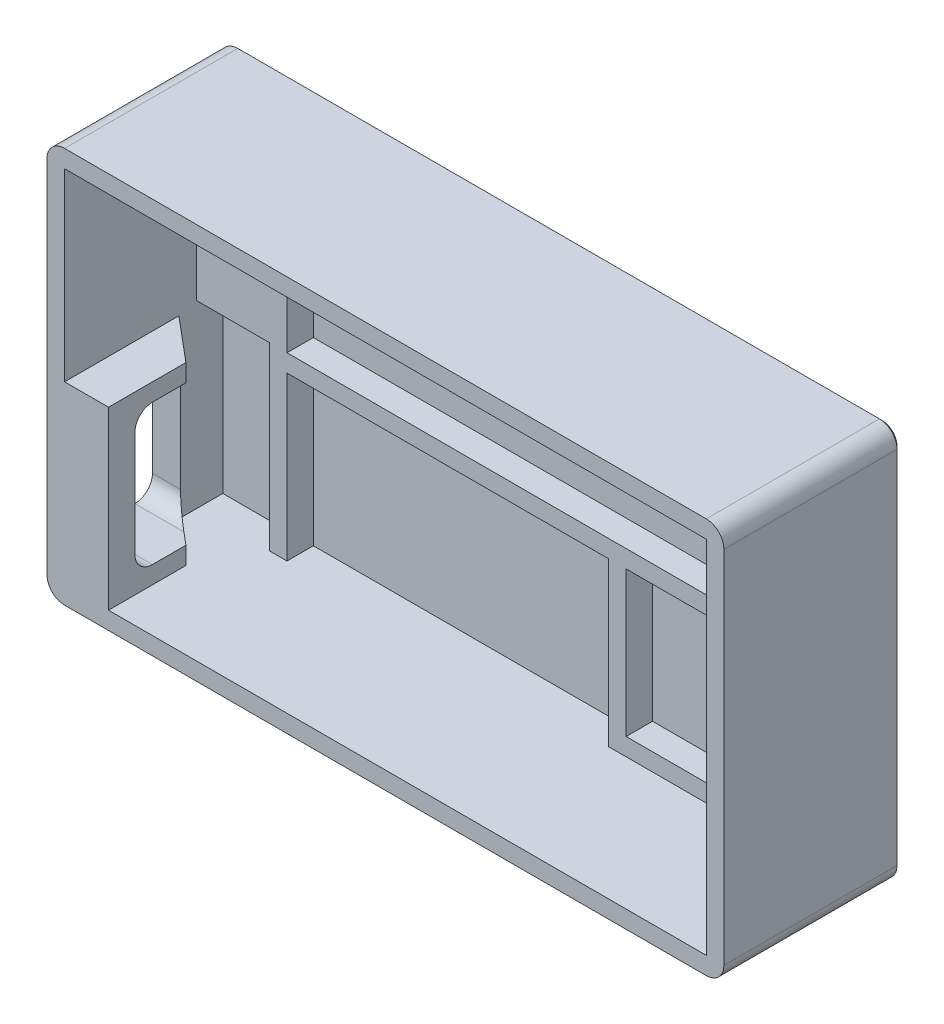
SolidWorks part; units mm, degrees
material "Custom Plastic"
ref_plane "Front Plane" through (0, 0, 0) normal (0, 0, 1) x (1, 0, 0)
ref_plane "Top Plane" through (0, 0, 0) normal (0, 1, 0) x (1, 0, 0)
ref_plane "Right Plane" through (0, 0, 0) normal (1, 0, 0) x (0, 0, -1)
sketch "Sketch1" plane through (0, 0, 0) normal (0, 0, 1) x (1, 0, 0)
  line L0 (47.9984, -22.6009) -> (51.1988, -25.8013) construction
  line L1 (51.1988, -22.6009) -> (47.9984, -25.8013) construction
  line L2 (8.5014, -16.2535) -> (10.4978, -18.2499) construction
  line L3 (10.4978, -16.2535) -> (8.5014, -18.2499) construction
  line L4 (30.1981, -17.239) -> (31.7221, -18.763) construction
  line L5 (31.7221, -17.239) -> (30.1981, -18.763) construction
  line L8 (30.1981, -17.239) -> (30.1981, -18.763)
  line L9 (30.1981, -18.763) -> (31.7221, -18.763)
  line L10 (31.7221, -18.763) -> (31.7221, -17.239)
  line L11 (31.7221, -17.239) -> (30.1981, -17.239)
  line L12 (10.4978, -16.2535) -> (8.5014, -16.2535)
  line L13 (8.5014, -16.2535) -> (8.5014, -18.2499)
  line L14 (8.5014, -18.2499) -> (10.4978, -18.2499)
  line L15 (10.4978, -18.2499) -> (10.4978, -16.2535)
  line L16 (47.9984, -22.6009) -> (47.9984, -25.8013)
  line L17 (47.9984, -25.8013) -> (51.1988, -25.8013)
  line L18 (51.1988, -25.8013) -> (51.1988, -22.6009)
  line L19 (51.1988, -22.6009) -> (47.9984, -22.6009)
  line L1295 (-5.0013, 10.0001) -> (66.9987, 10.0001)
  line L1296 (-5.0013, 10.0001) -> (-5.0013, -29.9999)
  line L1297 (-5.0013, -29.9999) -> (66.9987, -29.9999)
  line L1298 (66.9987, 10.0001) -> (66.9987, -29.9999)
  circle A0 centre (33.5001, -18.001) radius 0.762
  circle A1 centre (36.0401, -18.001) radius 0.762
  circle A2 centre (53.5203, -7.5108) radius 1.4478
  circle A3 centre (49.3217, -7.5108) radius 1.4478
  circle A4 centre (45.1206, -7.5108) radius 1.4478
  circle A5 centre (40.9219, -7.5108) radius 1.4478
  circle A6 centre (36.7208, -7.5108) radius 1.4478
  circle A7 centre (32.5222, -7.5108) radius 1.4478
  circle A8 centre (28.3235, -7.5108) radius 1.4478
  circle A9 centre (24.1249, -7.5108) radius 1.4478
  circle A10 centre (19.9238, -7.5108) radius 1.4478
  circle A11 centre (15.7251, -7.5108) radius 1.4478
  circle A12 centre (11.524, -7.5108) radius 1.4478
  circle A13 centre (7.3228, -7.5108) radius 1.4478
  circle A14 centre (53.5203, -2.0117) radius 1.4478
  circle A15 centre (49.3217, -2.0117) radius 1.4478
  circle A16 centre (45.1206, -2.0117) radius 1.4478
  circle A17 centre (40.9219, -2.0117) radius 1.4478
  circle A18 centre (36.7208, -2.0117) radius 1.4478
  circle A19 centre (32.5222, -2.0117) radius 1.4478
  circle A20 centre (28.3235, -2.0117) radius 1.4478
  circle A21 centre (24.1249, -2.0117) radius 1.4478
  circle A22 centre (19.9238, -2.0117) radius 1.4478
  circle A23 centre (15.7251, -2.0117) radius 1.4478
  circle A24 centre (11.524, -2.0117) radius 1.4478
  circle A25 centre (7.3228, -2.0117) radius 1.4478
  circle A26 centre (7.3076, 4.699) radius 0.889
  circle A27 centre (25.0876, 4.699) radius 0.889
  circle A28 centre (53.3883, 4.8997) radius 0.889
  circle A29 centre (35.6083, 4.8997) radius 0.889
  circle A30 centre (26.0985, -19.0906) radius 0.6985
  circle A31 centre (26.0985, -26.7106) radius 0.6985
  circle A32 centre (20.4978, -19.0906) radius 0.6985
  circle A33 centre (20.4978, -26.7106) radius 0.6985
  circle A34 centre (26.0985, -14.031) radius 0.8382
  circle A35 centre (26.0985, -16.571) radius 0.8382
  circle A36 centre (20.4978, -13.9319) radius 0.8382
  circle A37 centre (20.4978, -16.4719) radius 0.8382
  circle A38 centre (9.4996, -24.7498) radius 1.2497
  circle A39 centre (-0.0013, 0.0001) radius 3.0988
  circle A40 centre (61.9987, -19.9999) radius 3.0988
  circle A41 centre (53.7997, -24.2011) radius 1.6002
  circle A42 centre (49.5986, -18.702) radius 1.6002
  circle A43 centre (53.7997, -18.702) radius 1.6002
  dimension "D1" = 62
  dimension "D2" = 72
  dimension "D3" = 40
  dimension "D4" = 5
  dimension "D5" = 10
  dimension "D6" = 20
sketch "Sketch2" plane through (0, 0, 0) normal (0, 0, 1) x (1, 0, 0)
  line L0 (-5.0013, 10.0001) -> (-5.5013, 10.5001) construction
  line L1 (-5.5013, 10.5001) -> (67.4987, 10.5001) construction
  line L2 (-5.5013, 10.5001) -> (-5.5013, -30.4999) construction
  line L3 (-5.5013, -30.4999) -> (67.4987, -30.4999) construction
  line L4 (67.4987, 10.5001) -> (67.4987, -30.4999) construction
  line L5 (-7.5013, 12.5001) -> (69.4987, 12.5001)
  line L6 (-7.5013, 12.5001) -> (-7.5013, -32.4999)
  line L7 (-7.5013, -32.4999) -> (69.4987, -32.4999)
  line L8 (69.4987, 12.5001) -> (69.4987, -32.4999)
  line L9 (-5.5013, 10.5001) -> (-7.5013, 12.5001) construction
  line L10 (66.9987, -29.9999) -> (67.4987, -30.4999) construction
  line L11 (67.4987, -30.4999) -> (69.4987, -32.4999) construction
  line L12 (-5.0013, 10.0001) -> (-5.0013, 10.5001) construction
  line L13 (-5.0013, 10.0001) -> (-5.5013, 10.0001) construction
  line L14 (66.9987, -30.4999) -> (66.9987, -29.9999) construction
  line L15 (66.9987, -29.9999) -> (67.4987, -29.9999) construction
  line L16 (-5.0013, 10.0001) -> (66.9987, 10.0001) construction
  circle A0 centre (-0.0013, 0.0001) radius 2.1
  circle A1 centre (61.9987, -19.9999) radius 2.1
  circle A4 centre (61.9987, -19.9999) radius 3.0988 construction
  dimension "D3" = 4.2
  dimension "D1" = 0.5
  dimension "D2" = 2
extrude "Boss-Extrude2" add sketch "Sketch2" along normal blind 20
sketch "Sketch3" plane through (0, 0, 20) normal (0, 0, 1) x (1, 0, 0)
  line L0 (-5.0013, 10.0001) -> (66.9987, 10.0001) construction
  line L1 (-5.5013, 10.5001) -> (67.4987, 10.5001)
  line L2 (-5.5013, 10.5001) -> (-5.5013, -10.4999)
  line L3 (-0.5013, -30.4999) -> (67.4987, -30.4999)
  line L4 (67.4987, 10.5001) -> (67.4987, -30.4999)
  line L5 (-5.0013, 10.0001) -> (-5.0013, 10.5001) construction
  line L6 (-5.0013, 10.0001) -> (-5.5013, 10.0001) construction
  line L7 (66.9987, -29.9999) -> (66.9987, -30.4999) construction
  line L8 (66.9987, -29.9999) -> (67.4987, -29.9999) construction
  line L9 (-0.5013, -30.4999) -> (-0.5013, -10.4999)
  line L10 (-0.5013, -10.4999) -> (-5.5013, -10.4999)
  dimension "D1" = 0.5
  dimension "D2" = 20
  dimension "D3" = 5
extrude "Cut-Extrude1" cut sketch "Sketch3" against normal offset from surface (15 mm away) 5 up to face at (2.0987, 0.0001, 0)
sketch "Sketch4" plane through (0, 0, 5) normal (0, 0, 1) x (1, 0, 0)
  line L0 (4.8021, 10.5001) -> (4.8021, -9.9845)
  line L1 (4.8021, 10.5001) -> (57.1818, 10.5001)
  line L2 (4.8021, -11.9845) -> (4.8021, -30.4999)
  line L3 (4.8021, -30.4999) -> (41.3831, -30.4999)
  line L4 (57.1818, -11.9845) -> (57.1818, -28.4999)
  line L5 (57.1818, 10.5001) -> (57.1818, -9.9845)
  line L6 (4.8021, -11.9845) -> (41.3831, -11.9845)
  line L7 (57.1818, -9.9845) -> (4.8021, -9.9845)
  line L8 (43.3831, -28.4999) -> (43.3831, -11.9845)
  line L9 (41.3831, -11.9845) -> (41.3831, -30.4999)
  line L10 (43.3831, -28.4999) -> (57.1818, -28.4999)
  line L11 (43.3831, -11.9845) -> (57.1818, -11.9845)
  line L12 (57.1818, -11.9845) -> (57.1818, -9.9845) construction
  line L13 (57.1818, -28.4999) -> (57.1818, -30.4999) construction
  line L14 (67.4987, -30.4999) -> (-0.5013, -30.4999) construction
  line L15 (43.3831, -11.9845) -> (41.3831, -11.9845) construction
  line L16 (57.1818, -9.9845) -> (59.1818, -9.9845) construction
  line L17 (67.4987, 10.5001) -> (59.1818, 10.5001)
  line L18 (67.4987, 10.5001) -> (67.4987, -11.9845)
  line L19 (67.4987, -11.9845) -> (59.1818, -11.9845)
  line L20 (59.1818, 10.5001) -> (59.1818, -11.9845)
  line L21 (2.8021, -9.9845) -> (4.8021, -9.9845) construction
  line L22 (-5.5013, -30.4999) -> (2.8021, -30.4999)
  line L23 (-5.5013, -30.4999) -> (-5.5013, -9.9845)
  line L24 (-5.5013, -9.9845) -> (2.8021, -9.9845)
  line L25 (2.8021, -30.4999) -> (2.8021, -9.9845)
  circle A0 centre (-0.0013, 0.0001) radius 2.1
  circle A1 centre (61.9987, -19.9999) radius 2.1
  circle A4 centre (61.9987, -19.9999) radius 2.1 construction
  circle A5 centre (-0.0013, 0.0001) radius 2.1 construction
  dimension "D1" = 2
extrude "Cut-Extrude2" cut sketch "Sketch4" against normal offset from surface (3 mm away) 2 up to face at (2.0987, 0.0001, 0)
sketch "Sketch5" plane through (-7.5013, 0, 0) normal (-1, 0, 0) x (0, 0, 1)
  line L0 (5, -30.4999) -> (5, -10.4999) construction
  line L1 (10, -12.4999) -> (15, -12.4999)
  line L2 (8, -14.4999) -> (8, -26.4999)
  line L3 (10, -28.4999) -> (15, -28.4999)
  line L4 (17, -14.4999) -> (17, -26.4999)
  line L5 (5, -30.4999) -> (20, -30.4999) construction
  arc A0 (17, -26.4999) -> (15, -28.4999) centre (15, -26.4999) cw
  arc A1 (10, -28.4999) -> (8, -26.4999) centre (10, -26.4999) cw
  arc A2 (10, -12.4999) -> (8, -14.4999) centre (10, -14.4999) ccw
  arc A3 (15, -12.4999) -> (17, -14.4999) centre (15, -14.4999) cw
  dimension "D3" = 2
  dimension "D5" = 2
  dimension "D6" = 2
  dimension "D7" = 2
  dimension "D1" = 3
  dimension "D2" = 12
  dimension "D4" = 2
  dimension "D8" = 16
extrude "Cut-Extrude3" cut sketch "Sketch5" against normal up to next
fillet "Fillet1" radius 2 4 edges at (69.4987, -32.4999, 10) (69.4987, 12.5001, 10) (-7.5013, 12.5001, 10) (-7.5013, -32.4999, 10)
sketch "Sketch6" plane through (0, -10.4999, 0) normal (0, 1, 0) x (1, 0, 0)
  line L0 (-5.5013, -7) -> (-0.5013, -11.1955)
  line L1 (-5.5013, 0) -> (-5.5013, -20) construction
  line L2 (-0.5013, -5) -> (-0.5013, -20) construction
  line L5 (-5.5013, -5) -> (4.8021, -5) construction
  line L6 (-5.5013, -7) -> (-5.5013, -5)
  line L7 (-5.5013, -5) -> (-0.5013, -5)
  line L8 (-0.5013, -5) -> (-0.5013, -11.1955)
  dimension "D1" = 2
  dimension "D2" = 50
extrude "Cut-Extrude8" cut sketch "Sketch6" against normal blind 20
chamfer "Chamfer1" distance 0.3 angle 45 10 edges at (64.0987, -19.9999, 0) (68.913, 11.9143, 0) (30.9987, 12.5001, 0) (-6.9155, 11.9143, 0) (-7.5013, -9.9999, 0) (-6.9155, -31.9142, 0) (30.9987, -32.4999, 0) (68.913, -31.9142, 0) (69.4987, -9.9999, 0) (2.0987, 0.0001, 0)
